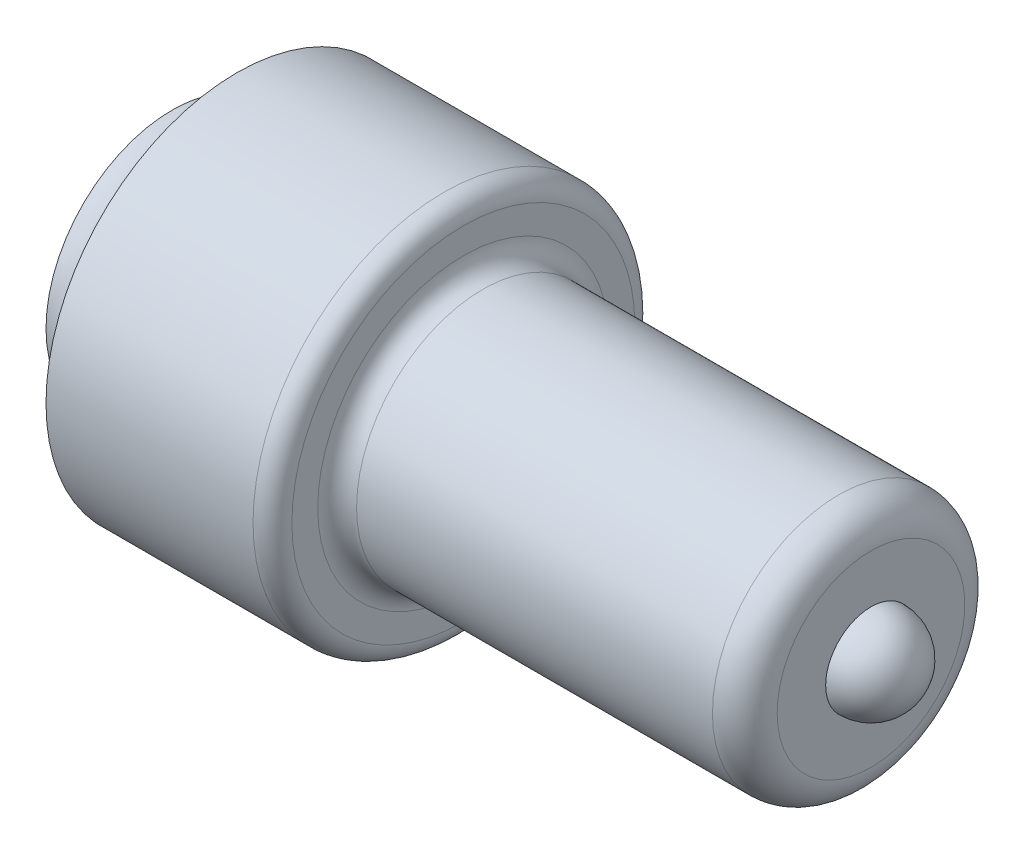
SolidWorks part; units mm, degrees
ref_plane "Front Plane" through (0, 0, 0) normal (0, 0, 1) x (1, 0, 0)
ref_plane "Top Plane" through (0, 0, 0) normal (0, 1, 0) x (1, 0, 0)
ref_plane "Right Plane" through (0, 0, 0) normal (1, 0, 0) x (0, 0, -1)
sketch "Sketch1" plane through (0, 0, 0) normal (0, 0, 1) x (1, 0, 0)
  line L0 (0, 0) -> (146.05, 0)
  line L16 (0, 0) -> (0, 24.765)
  line L18 (12.7, 37.465) -> (53.34, 37.465)
  line L20 (57.15, 33.655) -> (57.15, 28.575)
  line L21 (60.96, 24.765) -> (130.81, 24.765)
  line L22 (137.16, 18.415) -> (137.16, 8.89)
  arc A2 (146.05, 0) -> (137.16, 8.89) centre (137.16, 0) ccw
  arc A3 (0, 24.765) -> (12.7, 37.465) centre (0, 37.465) ccw
  arc A4 (130.81, 24.765) -> (137.16, 18.415) centre (130.81, 18.415) cw
  arc A5 (57.15, 28.575) -> (60.96, 24.765) centre (60.96, 28.575) ccw
  arc A6 (53.34, 37.465) -> (57.15, 33.655) centre (53.34, 33.655) cw
  point P16 (57.15, 37.465)
  dimension "D3" = 3.81
  dimension "D2" = 6.35
  dimension "D1" = 146.05
revolve "Revolve5" add sketch "Sketch1" angle 360 about L0
